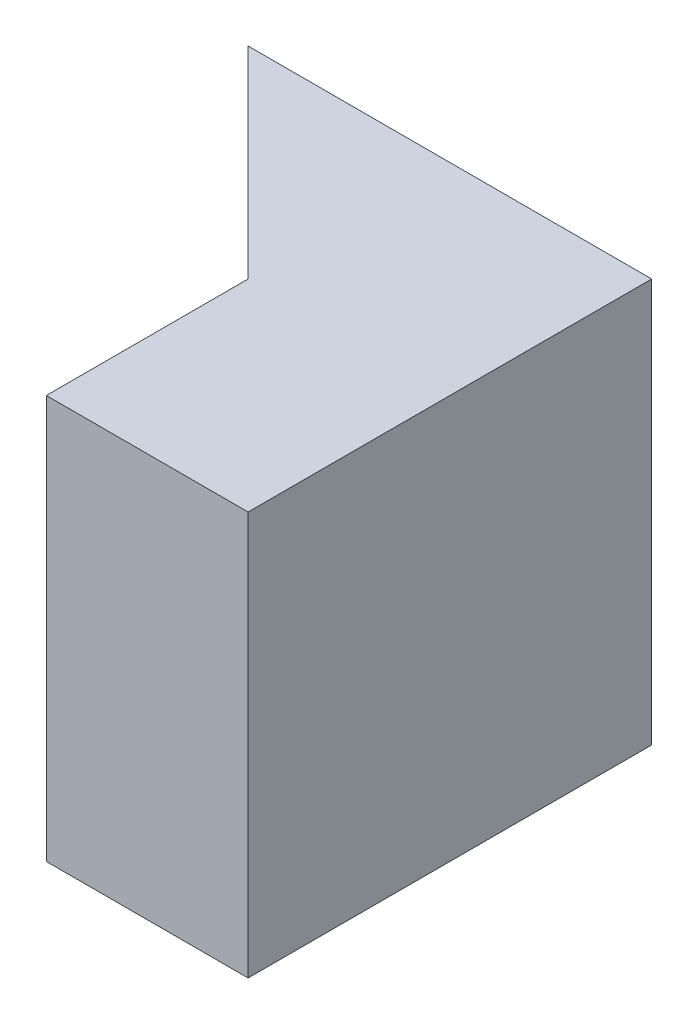
SolidWorks part; units mm, degrees
ref_plane "Front Plane" through (0, 0, 0) normal (0, 0, 1) x (1, 0, 0)
ref_plane "Top Plane" through (0, 0, 0) normal (0, 1, 0) x (1, 0, 0)
ref_plane "Right Plane" through (0, 0, 0) normal (1, 0, 0) x (0, 0, -1)
sketch "Sketch1" plane through (0, 0, 0) normal (0, 0, 1) x (1, 0, 0)
  line L1 (0, 0) -> (20, 0)
  line L2 (0, 0) -> (0, 20)
  line L3 (0, 20) -> (20, 20)
  line L4 (20, 0) -> (20, 20)
  dimension "D1" = 20
  dimension "D2" = 20
extrude "Boss-Extrude1" add sketch "Sketch1" along normal blind 20
sketch "Sketch2" plane through (0, 20, 0) normal (0, 1, 0) x (1, 0, 0)
  line L1 (0, -20) -> (10, -20)
  line L2 (0, -20) -> (0, -10)
  line L3 (0, -10) -> (10, -10)
  line L4 (10, -20) -> (10, -10)
  dimension "D1" = 10
  dimension "D2" = 10
extrude "Cut-Extrude1" cut sketch "Sketch2" against normal blind 20
sketch "Sketch3" plane through (0, 20, 0) normal (0, 1, 0) x (1, 0, 0)
  line L0 (0, 0) -> (10, -10)
  line L1 (10, -10) -> (0, -10)
  line L2 (0, -10) -> (0, 0)
extrude "Cut-Extrude2" cut sketch "Sketch3" against normal blind 20
